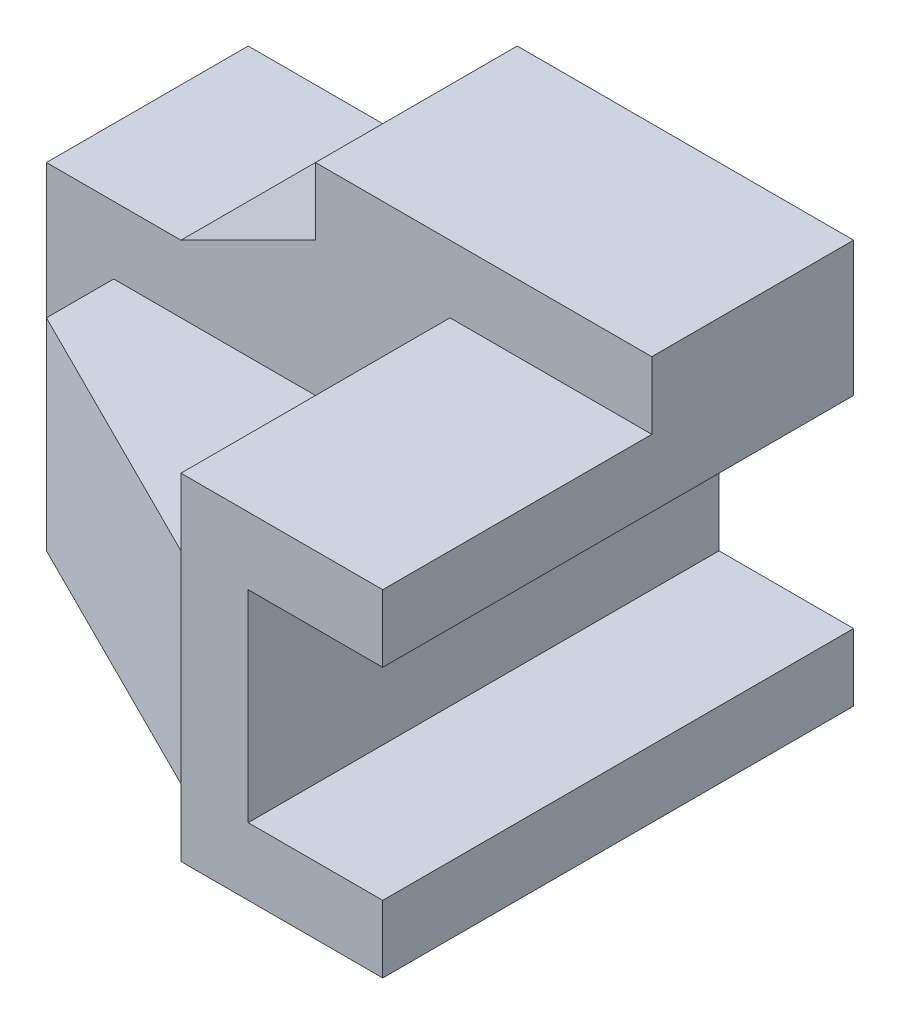
SolidWorks part; units mm, degrees
ref_plane "Front Plane" through (0, 0, 0) normal (0, 0, 1) x (1, 0, 0)
ref_plane "Top Plane" through (0, 0, 0) normal (0, 1, 0) x (1, 0, 0)
ref_plane "Right Plane" through (0, 0, 0) normal (1, 0, 0) x (0, 0, -1)
sketch "Sketch1" plane through (0, 0, 0) normal (0, 1, 0) x (1, 0, 0)
  line L0 (0, 0) -> (90, 0)
  line L1 (90, 0) -> (90, -70)
  line L2 (90, -70) -> (60, -70)
  line L3 (60, -70) -> (60, -60)
  line L4 (60, -60) -> (50, -60)
  line L5 (50, -60) -> (10, -40)
  line L6 (10, -40) -> (10, -30)
  line L7 (10, -30) -> (0, -30)
  line L8 (0, -30) -> (0, 0)
  dimension "D1" = 70
  dimension "D2" = 30
  dimension "D3" = 10
  dimension "D4" = 10
  dimension "D5" = 10
  dimension "D6" = 10
  dimension "D7" = 30
  dimension "D8" = 90
extrude "Boss-Extrude1" add sketch "Sketch1" along normal blind 30
sketch "Sketch3" plane through (0, 30, 0) normal (0, 1, 0) x (1, 0, 0)
  line L0 (0, 0) -> (90, 0)
  line L1 (90, 0) -> (90, -70)
  line L2 (90, -70) -> (60, -70)
  line L3 (60, -70) -> (60, -30)
  line L4 (60, -30) -> (0, -30)
  line L6 (0, 0) -> (0, -30) construction
  line L7 (0, -30) -> (0, 0)
  dimension "D1" = 30
  dimension "D2" = 40
extrude "Boss-Extrude2" add sketch "Sketch3" along normal blind 30
sketch "Sketch5" plane through (0, 0, 70) normal (0, 0, 1) x (1, 0, 0)
  line L0 (90, 60) -> (90, 0) construction
  line L1 (90, 10) -> (70, 10)
  line L2 (90, 10) -> (90, 40)
  line L3 (90, 40) -> (70, 40)
  line L4 (70, 10) -> (70, 40)
  line L5 (60, 0) -> (90, 0) construction
  dimension "D1" = 30
  dimension "D2" = 20
  dimension "D3" = 10
extrude "Cut-Extrude1" cut sketch "Sketch5" against normal through all
sketch "Sketch6" plane through (0, 0, 70) normal (0, 0, 1) x (1, 0, 0)
  line L0 (60, 60) -> (60, 0) construction
  line L1 (90, 60) -> (60, 60)
  line L2 (90, 60) -> (90, 50)
  line L3 (90, 50) -> (60, 50)
  line L4 (60, 60) -> (60, 50)
  dimension "D1" = 10
extrude "Cut-Extrude2" cut sketch "Sketch6" against normal blind 40
sketch "Sketch7" plane through (0, 0, 0) normal (0, 0, -1) x (-1, 0, 0)
  line L0 (-40, 60) -> (-40, 50)
  line L1 (-90, 60) -> (0, 60) construction
  line L2 (-40, 50) -> (-20, 40)
  line L3 (-20, 40) -> (0, 40)
  line L4 (0, 60) -> (0, 0) construction
  line L5 (0, 40) -> (0, 60)
  line L6 (0, 60) -> (-40, 60)
  dimension "D1" = 10
  dimension "D2" = 20
  dimension "D3" = 10
  dimension "D4" = 20
extrude "Cut-Extrude3" cut sketch "Sketch7" against normal through all
